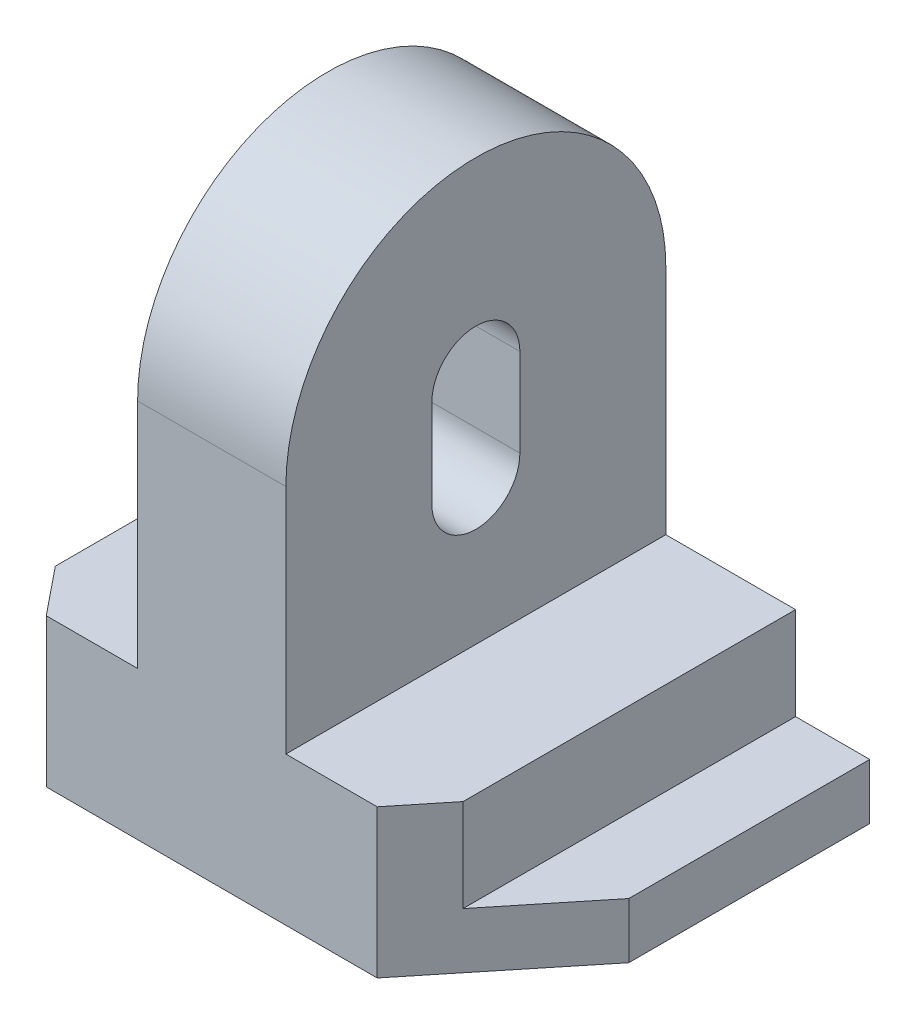
SolidWorks part; units mm, degrees
ref_plane "Front Plane" through (0, 0, 0) normal (0, 0, 1) x (1, 0, 0)
ref_plane "Top Plane" through (0, 0, 0) normal (0, 1, 0) x (1, 0, 0)
ref_plane "Right Plane" through (0, 0, 0) normal (1, 0, 0) x (0, 0, -1)
sketch "Sketch1" plane through (0, 0, 0) normal (0, 0, 1) x (1, 0, 0)
  line L0 (-60, 0) -> (60, 0)
  line L1 (60, 0) -> (60, 12)
  line L2 (60, 12) -> (44, 12)
  line L3 (44, 12) -> (44, 32)
  line L4 (44, 32) -> (16, 32)
  line L5 (16, 32) -> (16, 123)
  line L14 (-60, 0) -> (-60, 12)
  line L15 (-60, 12) -> (-44, 12)
  line L16 (-44, 12) -> (-44, 32)
  line L17 (-44, 32) -> (-16, 32)
  line L18 (-16, 32) -> (-16, 123)
  line L19 (-16, 123) -> (16, 123)
  dimension "D2" = 12
  dimension "D3" = 20
  dimension "D4" = 28
  dimension "D5" = 91
  dimension "D6" = 32
extrude "Boss-Extrude1" add sketch "Sketch1" along normal blind 82
chamfer "Chamfer6" distance 30 angle 39 1 edges at (60, 6, 82)
chamfer "Chamfer7" distance 30 angle 39 1 edges at (-60, 6, 82)
sketch "Sketch8" plane through (16, 0, 0) normal (1, 0, 0) x (0, 0, -1)
  line L0 (-82, 82) -> (-41, 82)
  line L2 (-41, 82) -> (-41, 63) construction
  line L3 (-31.5, 82) -> (-31.5, 63)
  line L4 (-50.5, 82) -> (-50.5, 63)
  line L5 (-41, 82) -> (4.4329, 82)
  arc A0 (0, 82) -> (-82, 82) centre (-41, 82) ccw
  arc A1 (-31.5, 82) -> (-50.5, 82) centre (-41, 82) ccw
  arc A2 (-50.5, 63) -> (-31.5, 63) centre (-41, 63) ccw
  point P5 (-41, 72.5)
  point P12 (0, 0)
  point P13 (-82, 82)
  dimension "D1" = 50
  dimension "D2" = 41
  dimension "D4" = 19
  dimension "D5" = 19
extrude "Cut-Extrude2" cut sketch "Sketch8" against normal blind 82
